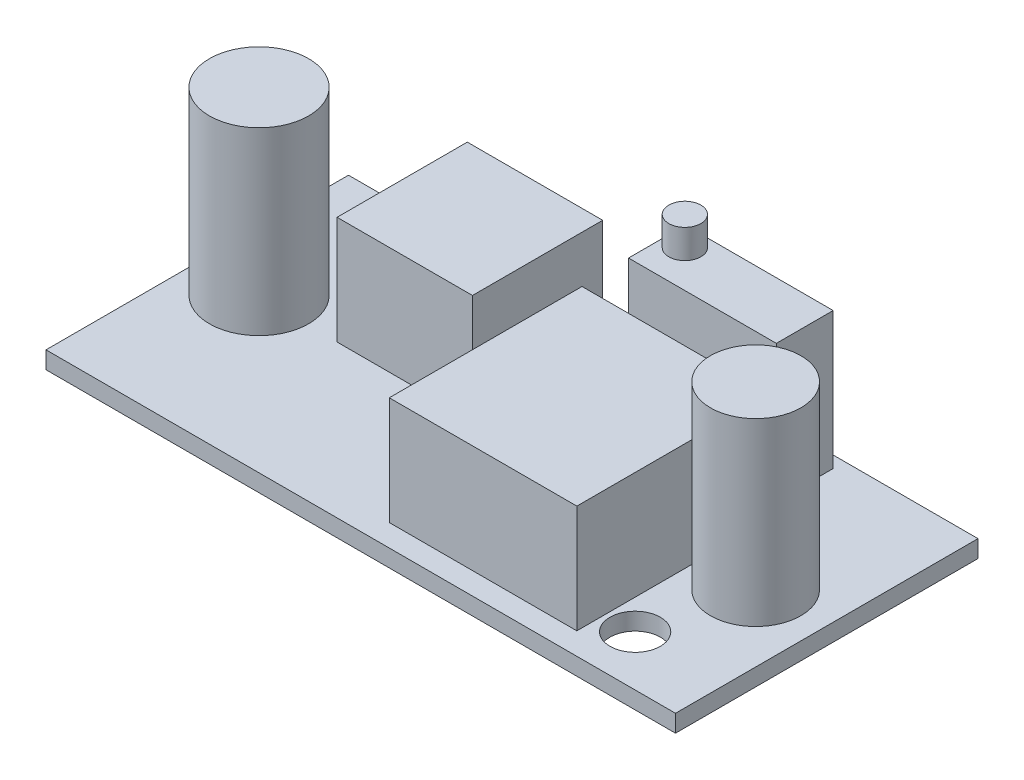
SolidWorks part; units mm, degrees
ref_plane "Front Plane" through (0, 0, 0) normal (0, 0, 1) x (1, 0, 0)
ref_plane "Top Plane" through (0, 0, 0) normal (0, 1, 0) x (1, 0, 0)
ref_plane "Right Plane" through (0, 0, 0) normal (1, 0, 0) x (0, 0, -1)
sketch "Sketch1" plane through (0, 0, 0) normal (0, 1, 0) x (1, 0, 0)
  line L1 (5.0803, -7.7821) -> (-38.6197, -7.7821)
  line L2 (5.0803, -7.7821) -> (5.0803, 13.2179)
  line L3 (5.0803, 13.2179) -> (-38.6197, 13.2179)
  line L4 (-38.6197, -7.7821) -> (-38.6197, 13.2179)
  dimension "D1" = 43.7
  dimension "D2" = 21
extrude "Boss-Extrude1" add sketch "Sketch1" along normal blind 1.2
sketch "Sketch2" plane through (0, 1.2, 0) normal (0, 1, 0) x (1, 0, 0)
  circle A0 centre (-34.5091, 2.8973) radius 3.4439
  circle A1 centre (0.4317, 2.4309) radius 3.1376
  point P4 (-34.5091, 2.8973)
extrude "Boss-Extrude2" add sketch "Sketch2" along normal blind 12.5
sketch "Sketch3" plane through (0, 1.2, 0) normal (0, 1, 0) x (1, 0, 0)
  line L1 (-16.3212, 7.1303) -> (-3.2992, 7.1303)
  line L2 (-16.3212, 7.1303) -> (-16.3212, -6.2505)
  line L3 (-16.3212, -6.2505) -> (-3.2992, -6.2505)
  line L4 (-3.2992, 7.1303) -> (-3.2992, -6.2505)
  line L5 (-28.9846, 11.8298) -> (-19.5857, 11.8298)
  line L6 (-28.9846, 11.8298) -> (-28.9846, 2.7896)
  line L7 (-28.9846, 2.7896) -> (-19.5857, 2.7896)
  line L8 (-19.5857, 11.8298) -> (-19.5857, 2.7896)
extrude "Boss-Extrude4" add sketch "Sketch3" along normal blind 7.5
sketch "Sketch4" plane through (0, 1.2, 0) normal (0, 1, 0) x (1, 0, 0)
  line L1 (-14.4199, 12.4037) -> (-4.1601, 12.4037)
  line L2 (-14.4199, 12.4037) -> (-14.4199, 8.4577)
  line L3 (-14.4199, 8.4577) -> (-4.1601, 8.4577)
  line L4 (-4.1601, 12.4037) -> (-4.1601, 8.4577)
extrude "Boss-Extrude5" add sketch "Sketch4" along normal blind 9.5 contours L2 L1 L4 L3
sketch "Sketch5" plane through (0, 10.7, 0) normal (0, 1, 0) x (1, 0, 0)
  circle A0 centre (-13.0926, 11.0405) radius 1.1121
extrude "Boss-Extrude6" add sketch "Sketch5" along normal blind 2
sketch "Sketch6" plane through (0, 1.2, 0) normal (0, 1, 0) x (1, 0, 0)
  line L0 (-38.6197, 13.2179) -> (-38.6197, -7.7821) construction
  line L1 (5.0803, 13.2179) -> (-38.6197, 13.2179) construction
  line L2 (5.0803, -7.7821) -> (5.0803, 13.2179) construction
  line L3 (-38.6197, -7.7821) -> (5.0803, -7.7821) construction
  circle A0 centre (-32.1197, 10.7179) radius 1.75
  circle A1 centre (-1.2197, -4.2821) radius 1.75
  dimension "D1" = 3.5
  dimension "D2" = 6.5
  dimension "D3" = 2.5
  dimension "D4" = 3.5
  dimension "D5" = 6.3
  dimension "D6" = 3.5
extrude "Cut-Extrude1" cut sketch "Sketch6" against normal blind 2
